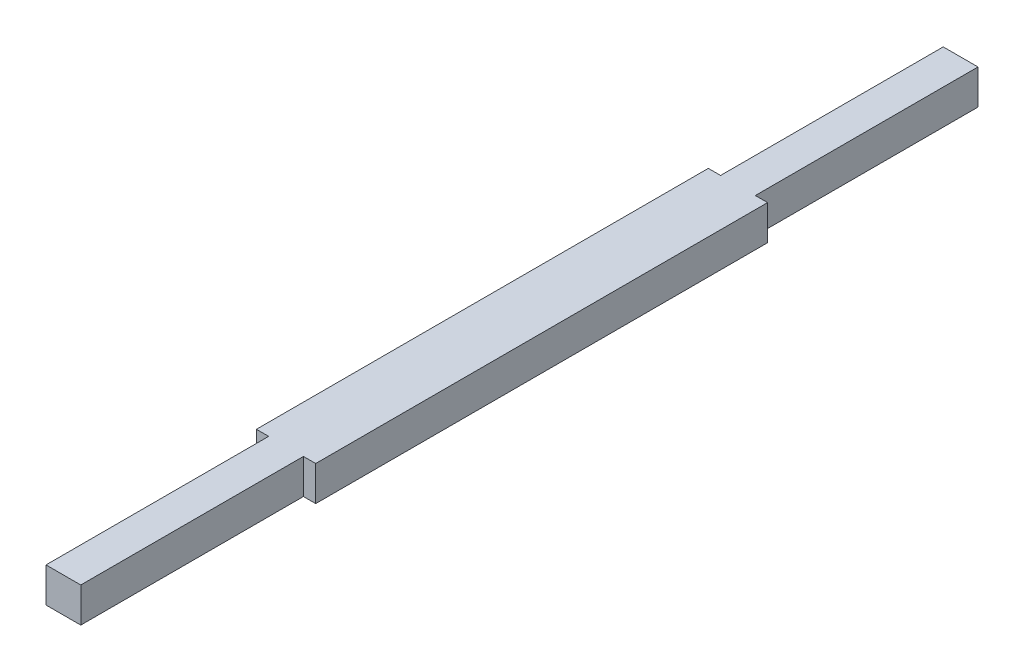
SolidWorks part; units mm, degrees
ref_plane "Front Plane" through (0, 0, 0) normal (0, 0, 1) x (1, 0, 0)
ref_plane "Top Plane" through (0, 0, 0) normal (0, 1, 0) x (1, 0, 0)
ref_plane "Right Plane" through (0, 0, 0) normal (1, 0, 0) x (0, 0, -1)
sketch "Sketch1" plane through (0, 0, 0) normal (0, 0, 1) x (1, 0, 0)
  line L1 (-4.5, -4.5) -> (4.5, -4.5)
  line L2 (-4.5, -4.5) -> (-4.5, 4.5)
  line L3 (-4.5, 4.5) -> (4.5, 4.5)
  line L4 (4.5, -4.5) -> (4.5, 4.5)
  line L5 (-4.5, -4.5) -> (4.5, 4.5) construction
  line L6 (-4.5, 4.5) -> (4.5, -4.5) construction
  point P0 (0, 0)
  dimension "D1" = 9
extrude "Boss-Extrude1" add sketch "Sketch1" along normal mid plane 232.3
sketch "Sketch2" plane through (0, 0, 0) normal (0, 1, 0) x (1, 0, 0)
  line L0 (4.5, -116.15) -> (4.5, 116.15) construction
  line L1 (4.5, 58.5) -> (7.675, 58.5)
  line L2 (4.5, 58.5) -> (4.5, -58.5)
  line L3 (4.5, -58.5) -> (7.675, -58.5)
  line L4 (7.675, 58.5) -> (7.675, -58.5)
  line L5 (-4.5, -116.15) -> (-4.5, 116.15) construction
  line L6 (-4.5, 58.5) -> (-7.675, 58.5)
  line L7 (-4.5, 58.5) -> (-4.5, -58.5)
  line L8 (-4.5, -58.5) -> (-7.675, -58.5)
  line L9 (-7.675, 58.5) -> (-7.675, -58.5)
  point P12 (7.675, 0)
  dimension "D1" = 3.175
  dimension "D2" = 117
extrude "Boss-Extrude2" add sketch "Sketch2" along normal mid plane 9
